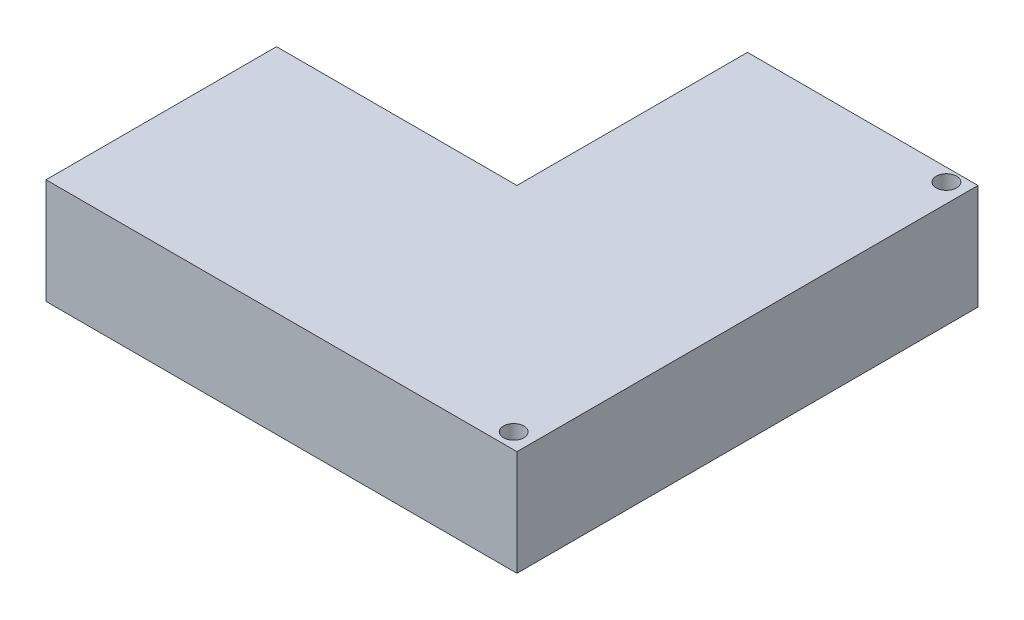
SolidWorks part; units mm, degrees
ref_plane "Front Plane" through (0, 0, 0) normal (0, 0, 1) x (1, 0, 0)
ref_plane "Top Plane" through (0, 0, 0) normal (0, 1, 0) x (1, 0, 0)
ref_plane "Right Plane" through (0, 0, 0) normal (1, 0, 0) x (0, 0, -1)
sketch "Sketch2" plane through (0, 0, 0) normal (0, -1, 0) x (1, 0, 0)
  line L0 (-13.7962, 46.5082) -> (-13.7962, -23.4918)
  line L1 (-13.7962, 46.5082) -> (-104.2962, 46.5082)
  line L2 (-13.7962, -23.4918) -> (-48.7962, -23.4918)
  line L4 (-104.2962, 46.5082) -> (-104.2962, 11.5082)
  line L5 (-104.2962, 11.5082) -> (-48.7962, 11.5082)
  line L6 (-48.7962, 11.5082) -> (-48.7962, -23.4918)
  dimension "D1" = 70
  dimension "D2" = 90.5
  dimension "D3" = 35
  dimension "D4" = 35
extrude "Boss-Extrude1" add sketch "Sketch2" along normal mid plane 16
other "Move Face1" face at (-104.2962, 0, 29.0082) parameters "D1"=19
sketch "Sketch3" plane through (0, -8, 0) normal (0, -1, 0) x (1, 0, 0)
  line L2 (-13.7962, -23.4918) -> (-13.7962, 46.5082) construction
  line L5 (-13.7962, 46.5082) -> (-85.2962, 46.5082) construction
  line L7 (-48.7962, -23.4918) -> (-13.7962, -23.4918) construction
  circle A0 centre (-16.6462, 44.1582) radius 1.55
  circle A1 centre (-16.6462, -21.5418) radius 1.55
  point P4 (0, 0)
  point P5 (-16.6503, 43.8138)
  dimension "D1" = 3.1
  dimension "D2" = 1.3
  dimension "D3" = 0.8
  dimension "D4" = 0.4
extrude "Cut-Extrude1" cut sketch "Sketch3" against normal through all
